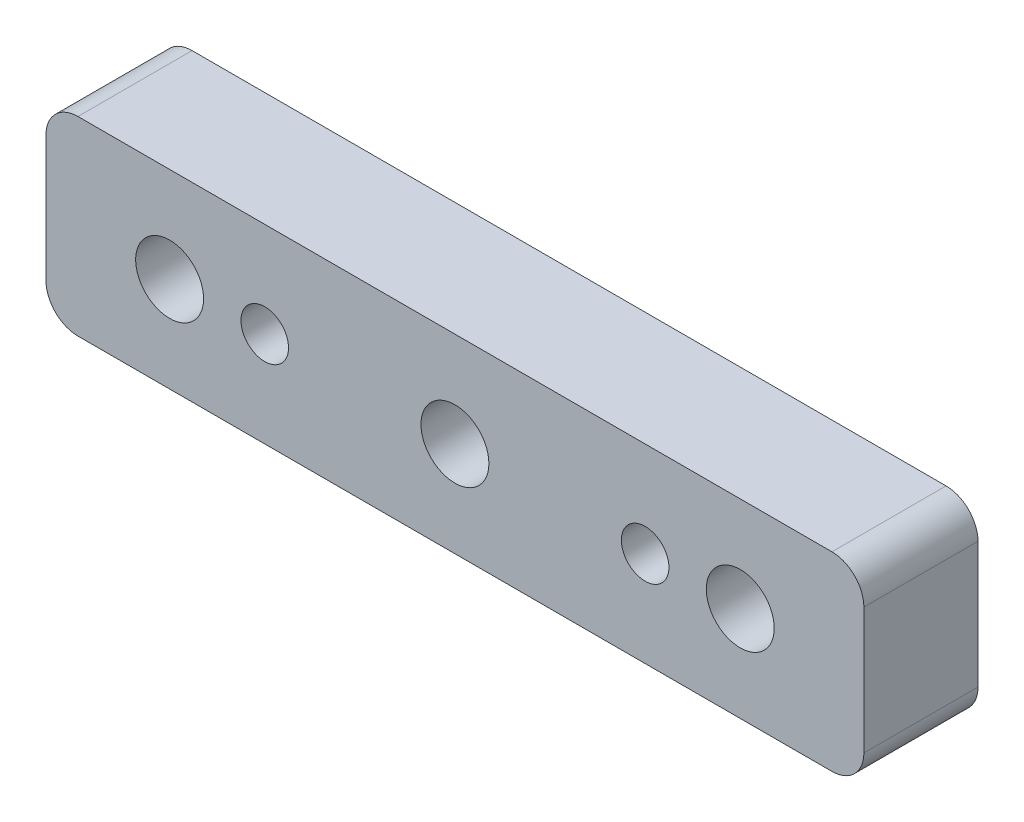
SolidWorks part; units mm, degrees
ref_plane "Front Plane" through (0, 0, 0) normal (0, 0, 1) x (1, 0, 0)
ref_plane "Top Plane" through (0, 0, 0) normal (0, 1, 0) x (1, 0, 0)
ref_plane "Right Plane" through (0, 0, 0) normal (1, 0, 0) x (0, 0, -1)
sketch "Sketch1" plane through (0, 0, 0) normal (0, 0, 1) x (1, 0, 0)
  line L0 (0, 0) -> (-20, 0) construction
  line L1 (-39.64, -10) -> (39.64, -10)
  line L2 (-43, -6.64) -> (-43, 6.64)
  line L3 (-39.64, 10) -> (39.64, 10)
  line L4 (43, -6.64) -> (43, 6.64)
  line L5 (-43, -10) -> (43, 10) construction
  line L6 (-43, 10) -> (43, -10) construction
  line L7 (-20, 0) -> (20, 0) construction
  circle A0 centre (-30, 0) radius 3.57
  circle A1 centre (0, 0) radius 3.57
  circle A2 centre (30, 0) radius 3.57
  circle A3 centre (-20, 0) radius 2.5
  circle A4 centre (20, 0) radius 2.5
  arc A5 (39.64, 10) -> (43, 6.64) centre (39.64, 6.64) cw
  arc A6 (39.64, -10) -> (43, -6.64) centre (39.64, -6.64) ccw
  arc A7 (-39.64, -10) -> (-43, -6.64) centre (-39.64, -6.64) cw
  arc A8 (-43, 6.64) -> (-39.64, 10) centre (-39.64, 6.64) cw
  point P0 (0, 0)
  dimension "D3" = 7.14
  dimension "D5" = 5
  dimension "D7" = 3.36
  dimension "D1" = 20
  dimension "D2" = 86
  dimension "D4" = 30
  dimension "D6" = 20
extrude "Boss-Extrude1" add sketch "Sketch1" along normal mid plane 12
